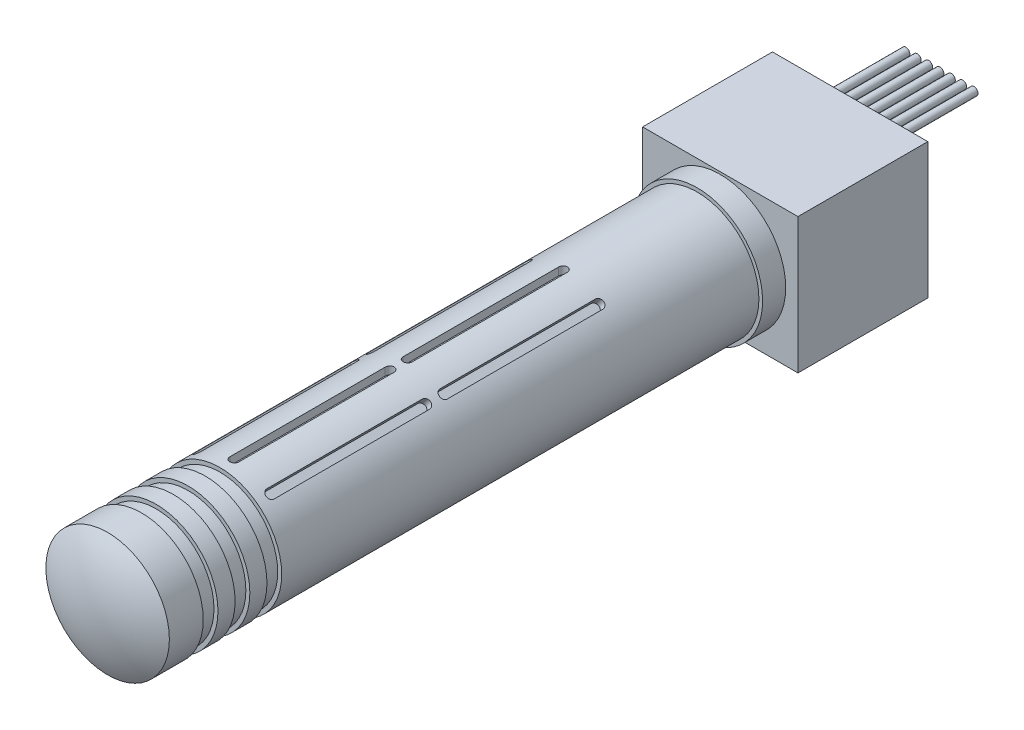
SolidWorks part; units mm, degrees
material "ABS"
ref_plane "Front Plane" through (0, 0, 0) normal (0, 0, 1) x (1, 0, 0)
ref_plane "Top Plane" through (0, 0, 0) normal (0, 1, 0) x (1, 0, 0)
ref_plane "Right Plane" through (0, 0, 0) normal (1, 0, 0) x (0, 0, -1)
sketch "Sketch1" plane through (0, 0, 0) normal (0, 0, 1) x (1, 0, 0)
  line L1 (9.906, -8.636) -> (-9.906, -8.636)
  line L2 (9.906, -8.636) -> (9.906, 8.636)
  line L3 (9.906, 8.636) -> (-9.906, 8.636)
  line L4 (-9.906, -8.636) -> (-9.906, 8.636)
  line L5 (9.906, -8.636) -> (-9.906, 8.636) construction
  line L6 (9.906, 8.636) -> (-9.906, -8.636) construction
  point P0 (0, 0)
  dimension "D1" = 19.812
  dimension "D2" = 17.272
extrude "Boss-Extrude1" add sketch "Sketch1" along normal blind 16.5608
sketch "Sketch2" plane through (0, 0, 0) normal (0, 0, -1) x (-1, 0, 0)
  line L0 (0, 8.636) -> (0, 5.7277) construction
  line L1 (-5.2578, 4.0894) -> (5.2578, 4.0894)
  line L2 (-5.2578, 4.0894) -> (-5.2578, 7.366)
  line L3 (-5.2578, 7.366) -> (5.2578, 7.366)
  line L4 (5.2578, 4.0894) -> (5.2578, 7.366)
  line L5 (-5.2578, 4.0894) -> (5.2578, 7.366) construction
  line L6 (-5.2578, 7.366) -> (5.2578, 4.0894) construction
  line L7 (-9.906, 8.636) -> (9.906, 8.636) construction
  point P0 (0, 5.7277)
  dimension "D1" = 10.5156
  dimension "D2" = 3.2766
  dimension "D3" = 4.5466
extrude "Boss-Extrude2" add sketch "Sketch2" along normal blind 1.27
sketch "Sketch3" plane through (0, 0, 16.5608) normal (0, 0, 1) x (1, 0, 0)
  circle A0 centre (0, 0) radius 8.3439
  dimension "D1" = 16.6878
extrude "Boss-Extrude3" add sketch "Sketch3" along normal blind 2.9464
sketch "Sketch4" plane through (0, 0, 19.5072) normal (0, 0, 1) x (1, 0, 0)
  circle A0 centre (0, 0) radius 7.874
  dimension "D1" = 15.748
extrude "Boss-Extrude4" add sketch "Sketch4" along normal blind 75.184
sketch "Sketch5" plane through (0, 0, 0) normal (0, 1, 0) x (1, 0, 0)
  line L0 (0, -94.6912) -> (0, -96.8502) construction
  line L1 (-7.874, -94.6912) -> (7.874, -94.6912) construction
  line L2 (9.906, 0) -> (-9.906, 0) construction
  line L3 (0, -96.8502) -> (0, -94.6912)
  line L4 (0, -94.6912) -> (7.874, -94.6912)
  line L5 (0, -96.8502) -> (-2.101, -96.8502) construction
  arc A0 (0, -96.8502) -> (7.874, -94.6912) centre (0, -81.4122) ccw
  dimension "D1" = 96.8502
revolve "Revolve1" add sketch "Sketch5" angle 360 about L3
sketch "Sketch6" plane through (0, 0, -1.27) normal (0, 0, -1) x (-1, 0, 0)
  line L0 (-5.2578, 5.7277) -> (5.2578, 5.7277) construction
  line L1 (-5.2578, 7.366) -> (-5.2578, 4.0894) construction
  line L2 (5.2578, 4.0894) -> (5.2578, 7.366) construction
  line L3 (-5.2578, 7.366) -> (-5.2578, 4.0894) construction
  circle A0 centre (-4.3688, 5.7277) radius 0.508
  dimension "D1" = 1.016
  dimension "D2" = 0.889
extrude "Wire" add sketch "Sketch6" along normal blind 10.16
pattern_linear "LPattern1" count 7 spacing 1.4478 along (-1, 0, 0) of "Wire"
sketch "Sketch7" plane through (0, 8.636, 0) normal (0, 1, 0) x (1, 0, 0)
  line L0 (0, -16.5608) -> (0, -36.6268) construction
  line L1 (-8.3439, -16.5608) -> (8.3439, -16.5608) construction
  line L2 (0, -36.6268) -> (0, -56.4388) construction
  line L3 (0.5715, -36.6268) -> (0.5715, -56.4388)
  line L4 (-0.5715, -36.6268) -> (-0.5715, -56.4388)
  line L5 (0, -58.7248) -> (0, -78.5368) construction
  line L6 (0.5715, -58.7248) -> (0.5715, -78.5368)
  line L7 (-0.5715, -58.7248) -> (-0.5715, -78.5368)
  line L8 (0.5715, -56.4388) -> (-0.5715, -56.4388) construction
  line L9 (-0.5715, -58.7248) -> (0.5715, -58.7248) construction
  arc A0 (0.5715, -36.6268) -> (-0.5715, -36.6268) centre (0, -36.6268) ccw
  arc A1 (-0.5715, -56.4388) -> (0.5715, -56.4388) centre (0, -56.4388) ccw
  arc A2 (0.5715, -58.7248) -> (-0.5715, -58.7248) centre (0, -58.7248) ccw
  arc A3 (-0.5715, -78.5368) -> (0.5715, -78.5368) centre (0, -78.5368) ccw
  point P5 (0, -46.5328)
  point P13 (0, -68.6308)
  dimension "D1" = 20.066
  dimension "D2" = 19.812
  dimension "D3" = 1.143
  dimension "D4" = 41.91
extrude "Cut-Extrude1" cut sketch "Sketch7" against normal blind 1.778
pattern_circular "CirPattern1" count 10 over 360 about axis through (0, 0, 0) along (0, 0, 1) skipping 2, 3, 7, 8 of "Cut-Extrude1"
ref_plane "Plane1" through (0, 0, 82.2452) normal (0, 0, 1) x (1, 0, 0)
sketch "Sketch8" plane through (0, 0, 82.2452) normal (0, 0, 1) x (1, 0, 0)
  circle A0 centre (0, 0) radius 7.874
  circle A1 centre (0, 0) radius 7.366
  circle A3 centre (0, 0) radius 7.874 construction
  dimension "D1" = 0.508
extrude "Cut-Extrude2" cut sketch "Sketch8" against normal blind 1.8796
pattern_linear "LPattern2" count 3 spacing 4.064 along (0, 0, 1) of "Cut-Extrude2"
